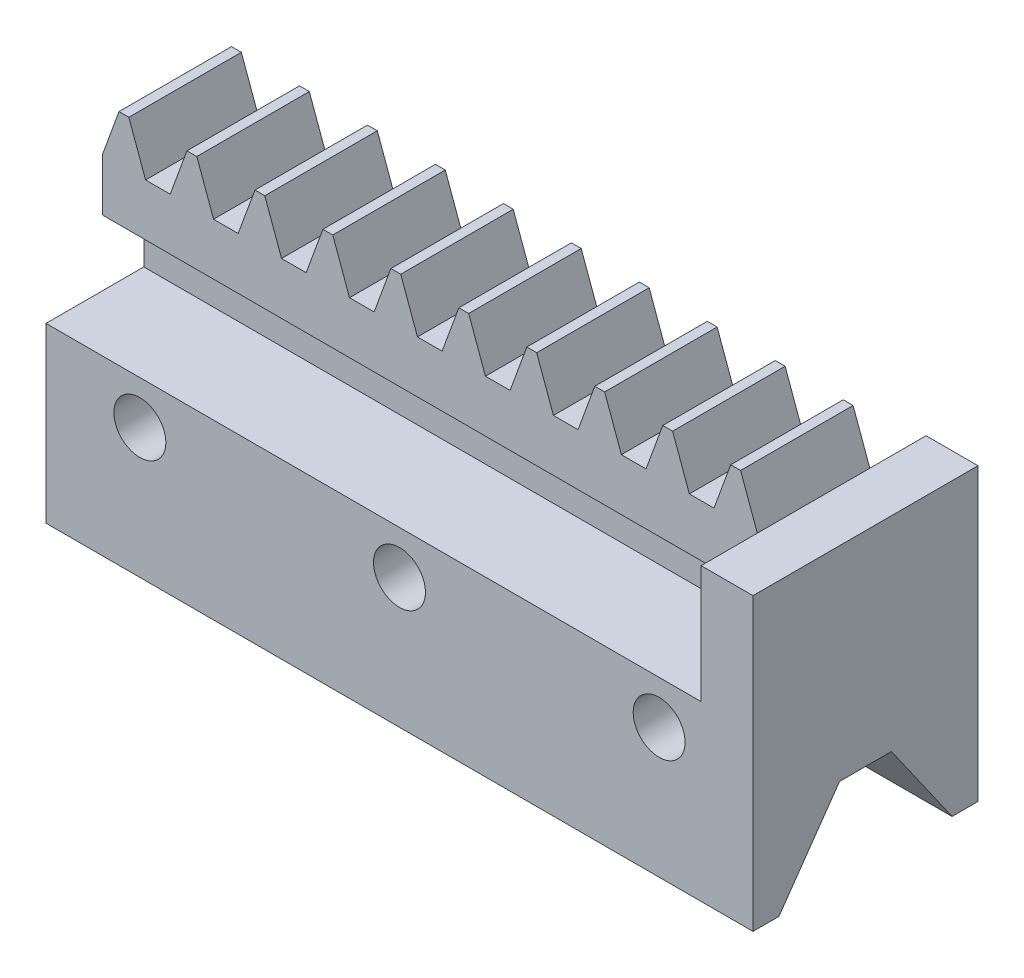
SolidWorks part; units mm, degrees
ref_plane "Plan de face" through (0, 0, 0) normal (0, 0, 1) x (1, 0, 0)
ref_plane "Plan de dessus" through (0, 0, 0) normal (0, 1, 0) x (1, 0, 0)
ref_plane "Plan de droite" through (0, 0, 0) normal (1, 0, 0) x (0, 0, -1)
sketch "Esquisse1" plane through (0, 0, 0) normal (0, 0, 1) x (1, 0, 0)
  circle A1 centre (0, 0) radius 2.5
  arc A192 (-2.7975, 7.3493) -> (-3.2186, 7.1749) centre (0, 0) ccw
  arc A193 (-3.7466, 7.3576) -> (-3.2186, 7.1749) centre (-3.3855, 7.5469) ccw
  arc A194 (-3.7466, 7.3576) -> (-5.4988, 8.9274) centre (-6.7243, 5.7967) ccw
  arc A195 (-5.4988, 8.9274) -> (-6.1435, 8.4966) centre (0, 0) ccw
  arc A196 (-6.1435, 8.4966) -> (-5.3638, 6.2771) centre (-2.7822, 8.4307) ccw
  arc A197 (-5.397, 5.7193) -> (-5.3638, 6.2771) centre (-5.6769, 6.0159) ccw
  arc A198 (-5.397, 5.7193) -> (-5.7193, 5.397) centre (0, 0) ccw
  arc A199 (-6.2771, 5.3638) -> (-5.7193, 5.397) centre (-6.0159, 5.6769) ccw
  arc A200 (-6.2771, 5.3638) -> (-8.4966, 6.1435) centre (-8.4307, 2.7822) ccw
  arc A201 (-8.4966, 6.1435) -> (-8.9274, 5.4988) centre (0, 0) ccw
  arc A202 (-8.9274, 5.4988) -> (-7.3576, 3.7466) centre (-5.7967, 6.7243) ccw
  arc A203 (-7.1749, 3.2186) -> (-7.3576, 3.7466) centre (-7.5469, 3.3855) ccw
  arc A204 (-7.1749, 3.2186) -> (-7.3493, 2.7975) centre (0, 0) ccw
  arc A205 (-7.8519, 2.5534) -> (-7.3493, 2.7975) centre (-7.7304, 2.9426) ccw
  arc A206 (-7.8519, 2.5534) -> (-10.2009, 2.4244) centre (-8.8537, -0.6559) ccw
  arc A207 (-10.2009, 2.4244) -> (-10.3521, 1.6639) centre (0, 0) ccw
  arc A208 (-10.3521, 1.6639) -> (-8.2313, 0.6458) centre (-7.9287, 3.9941) ccw
  arc A209 (-7.8604, 0.2279) -> (-8.2313, 0.6458) centre (-8.268, 0.2397) ccw
  arc A210 (-7.8604, 0.2279) -> (-7.8604, -0.2279) centre (0, 0) ccw
  arc A211 (-8.2313, -0.6458) -> (-7.8604, -0.2279) centre (-8.268, -0.2397) ccw
  arc A212 (-8.2313, -0.6458) -> (-10.3521, -1.6639) centre (-7.9287, -3.9941) ccw
  arc A213 (-10.3521, -1.6639) -> (-10.2009, -2.4244) centre (0, 0) ccw
  arc A214 (-10.2009, -2.4244) -> (-7.8519, -2.5534) centre (-8.8537, 0.6559) ccw
  arc A215 (-7.3493, -2.7975) -> (-7.8519, -2.5534) centre (-7.7304, -2.9426) ccw
  arc A216 (-7.3493, -2.7975) -> (-7.1749, -3.2186) centre (0, 0) ccw
  arc A217 (-7.3576, -3.7466) -> (-7.1749, -3.2186) centre (-7.5469, -3.3855) ccw
  arc A218 (-7.3576, -3.7466) -> (-8.9274, -5.4988) centre (-5.7967, -6.7243) ccw
  arc A219 (-8.9274, -5.4988) -> (-8.4966, -6.1435) centre (0, 0) ccw
  arc A220 (-8.4966, -6.1435) -> (-6.2771, -5.3638) centre (-8.4307, -2.7822) ccw
  arc A221 (-5.7193, -5.397) -> (-6.2771, -5.3638) centre (-6.0159, -5.6769) ccw
  arc A222 (-5.7193, -5.397) -> (-5.397, -5.7193) centre (0, 0) ccw
  arc A223 (-5.3638, -6.2771) -> (-5.397, -5.7193) centre (-5.6769, -6.0159) ccw
  arc A224 (-5.3638, -6.2771) -> (-6.1435, -8.4966) centre (-2.7822, -8.4307) ccw
  arc A225 (-6.1435, -8.4966) -> (-5.4988, -8.9274) centre (0, 0) ccw
  arc A226 (-5.4988, -8.9274) -> (-3.7466, -7.3576) centre (-6.7243, -5.7967) ccw
  arc A227 (-3.2186, -7.1749) -> (-3.7466, -7.3576) centre (-3.3855, -7.5469) ccw
  arc A228 (-3.2186, -7.1749) -> (-2.7975, -7.3493) centre (0, 0) ccw
  arc A229 (-2.5534, -7.8519) -> (-2.7975, -7.3493) centre (-2.9426, -7.7304) ccw
  arc A230 (-2.5534, -7.8519) -> (-2.4244, -10.2009) centre (0.6559, -8.8537) ccw
  arc A231 (-2.4244, -10.2009) -> (-1.6639, -10.3521) centre (0, 0) ccw
  arc A232 (-1.6639, -10.3521) -> (-0.6458, -8.2313) centre (-3.9941, -7.9287) ccw
  arc A233 (-0.2279, -7.8604) -> (-0.6458, -8.2313) centre (-0.2397, -8.268) ccw
  arc A234 (-0.2279, -7.8604) -> (0.2279, -7.8604) centre (0, 0) ccw
  arc A235 (0.6458, -8.2313) -> (0.2279, -7.8604) centre (0.2397, -8.268) ccw
  arc A236 (0.6458, -8.2313) -> (1.6639, -10.3521) centre (3.9941, -7.9287) ccw
  arc A237 (1.6639, -10.3521) -> (2.4244, -10.2009) centre (0, 0) ccw
  arc A238 (2.4244, -10.2009) -> (2.5534, -7.8519) centre (-0.6559, -8.8537) ccw
  arc A239 (2.7975, -7.3493) -> (2.5534, -7.8519) centre (2.9426, -7.7304) ccw
  arc A240 (2.7975, -7.3493) -> (3.2186, -7.1749) centre (0, 0) ccw
  arc A241 (3.7466, -7.3576) -> (3.2186, -7.1749) centre (3.3855, -7.5469) ccw
  arc A242 (3.7466, -7.3576) -> (5.4988, -8.9274) centre (6.7243, -5.7967) ccw
  arc A243 (5.4988, -8.9274) -> (6.1435, -8.4966) centre (0, 0) ccw
  arc A244 (6.1435, -8.4966) -> (5.3638, -6.2771) centre (2.7822, -8.4307) ccw
  arc A245 (5.397, -5.7193) -> (5.3638, -6.2771) centre (5.6769, -6.0159) ccw
  arc A246 (5.397, -5.7193) -> (5.7193, -5.397) centre (0, 0) ccw
  arc A247 (6.2771, -5.3638) -> (5.7193, -5.397) centre (6.0159, -5.6769) ccw
  arc A248 (6.2771, -5.3638) -> (8.4966, -6.1435) centre (8.4307, -2.7822) ccw
  arc A249 (8.4966, -6.1435) -> (8.9274, -5.4988) centre (0, 0) ccw
  arc A250 (8.9274, -5.4988) -> (7.3576, -3.7466) centre (5.7967, -6.7243) ccw
  arc A251 (7.1749, -3.2186) -> (7.3576, -3.7466) centre (7.5469, -3.3855) ccw
  arc A252 (7.1749, -3.2186) -> (7.3493, -2.7975) centre (0, 0) ccw
  arc A253 (7.8519, -2.5534) -> (7.3493, -2.7975) centre (7.7304, -2.9426) ccw
  arc A254 (7.8519, -2.5534) -> (10.2009, -2.4244) centre (8.8537, 0.6559) ccw
  arc A255 (10.2009, -2.4244) -> (10.3521, -1.6639) centre (0, 0) ccw
  arc A256 (10.3521, -1.6639) -> (8.2313, -0.6458) centre (7.9287, -3.9941) ccw
  arc A257 (7.8604, -0.2279) -> (8.2313, -0.6458) centre (8.268, -0.2397) ccw
  arc A258 (7.8604, -0.2279) -> (7.8604, 0.2279) centre (0, 0) ccw
  arc A259 (8.2313, 0.6458) -> (7.8604, 0.2279) centre (8.268, 0.2397) ccw
  arc A260 (8.2313, 0.6458) -> (10.3521, 1.6639) centre (7.9287, 3.9941) ccw
  arc A261 (10.3521, 1.6639) -> (10.2009, 2.4244) centre (0, 0) ccw
  arc A262 (10.2009, 2.4244) -> (7.8519, 2.5534) centre (8.8537, -0.6559) ccw
  arc A263 (7.3493, 2.7975) -> (7.8519, 2.5534) centre (7.7304, 2.9426) ccw
  arc A264 (7.3493, 2.7975) -> (7.1749, 3.2186) centre (0, 0) ccw
  arc A265 (7.3576, 3.7466) -> (7.1749, 3.2186) centre (7.5469, 3.3855) ccw
  arc A266 (7.3576, 3.7466) -> (8.9274, 5.4988) centre (5.7967, 6.7243) ccw
  arc A267 (8.9274, 5.4988) -> (8.4966, 6.1435) centre (0, 0) ccw
  arc A268 (8.4966, 6.1435) -> (6.2771, 5.3638) centre (8.4307, 2.7822) ccw
  arc A269 (5.7193, 5.397) -> (6.2771, 5.3638) centre (6.0159, 5.6769) ccw
  arc A270 (5.7193, 5.397) -> (5.397, 5.7193) centre (0, 0) ccw
  arc A271 (5.3638, 6.2771) -> (5.397, 5.7193) centre (5.6769, 6.0159) ccw
  arc A272 (5.3638, 6.2771) -> (6.1435, 8.4966) centre (2.7822, 8.4307) ccw
  arc A273 (6.1435, 8.4966) -> (5.4988, 8.9274) centre (0, 0) ccw
  arc A274 (5.4988, 8.9274) -> (3.7466, 7.3576) centre (6.7243, 5.7967) ccw
  arc A275 (3.2186, 7.1749) -> (3.7466, 7.3576) centre (3.3855, 7.5469) ccw
  arc A276 (3.2186, 7.1749) -> (2.7975, 7.3493) centre (0, 0) ccw
  arc A277 (2.5534, 7.8519) -> (2.7975, 7.3493) centre (2.9426, 7.7304) ccw
  arc A278 (2.5534, 7.8519) -> (2.4244, 10.2009) centre (-0.6559, 8.8537) ccw
  arc A279 (2.4244, 10.2009) -> (1.6639, 10.3521) centre (0, 0) ccw
  arc A280 (1.6639, 10.3521) -> (0.6458, 8.2313) centre (3.9941, 7.9287) ccw
  arc A281 (0.2279, 7.8604) -> (0.6458, 8.2313) centre (0.2397, 8.268) ccw
  arc A282 (0.2279, 7.8604) -> (-0.2279, 7.8604) centre (0, 0) ccw
  arc A283 (-0.6458, 8.2313) -> (-0.2279, 7.8604) centre (-0.2397, 8.268) ccw
  arc A284 (-0.6458, 8.2313) -> (-1.6639, 10.3521) centre (-3.9941, 7.9287) ccw
  arc A285 (-1.6639, 10.3521) -> (-2.4244, 10.2009) centre (0, 0) ccw
  arc A286 (-2.4244, 10.2009) -> (-2.5534, 7.8519) centre (0.6559, 8.8537) ccw
  arc A287 (-2.7975, 7.3493) -> (-2.5534, 7.8519) centre (-2.9426, 7.7304) ccw
  point P3 (0, -7.8638)
extrude "Boss.-Extru.1" add sketch "Esquisse1" along normal blind 1
sketch "Esquisse2" plane through (0, 0, 1) normal (0, 0, 1) x (1, 0, 0)
  line L0 (0, 0) -> (0, -9.25) construction
  line L1 (-0.114, -9.25) -> (-13.3501, -9.25) construction
  line L2 (-0.015, -9.2555) -> (3.6062, -7.9375) construction
  line L3 (0.2847, -8) -> (1.2514, -10.656)
  line L4 (-0.2847, -8) -> (-1.2514, -10.656)
  line L5 (-0.2847, -8) -> (0.2847, -8)
  line L6 (1.2514, -10.656) -> (2.6755, -10.656)
  line L7 (3.6422, -8) -> (2.6755, -10.656)
  line L8 (3.6422, -8) -> (4.2115, -8)
  line L9 (4.2115, -8) -> (5.1782, -10.656)
  line L10 (5.1782, -10.656) -> (6.6024, -10.656)
  line L11 (7.5691, -8) -> (6.6024, -10.656)
  line L12 (7.5691, -8) -> (8.1384, -8)
  line L13 (8.1384, -8) -> (9.1051, -10.656)
  line L14 (9.1051, -10.656) -> (10.5293, -10.656)
  line L15 (11.496, -8) -> (10.5293, -10.656)
  line L16 (11.496, -8) -> (12.0653, -8)
  line L17 (12.0653, -8) -> (13.032, -10.656)
  line L18 (13.032, -10.656) -> (14.4561, -10.656)
  line L19 (15.4228, -8) -> (14.4561, -10.656)
  line L20 (15.4228, -8) -> (15.9922, -8)
  line L21 (15.9922, -8) -> (16.9589, -10.656)
  line L22 (16.9589, -10.656) -> (18.383, -10.656)
  line L23 (19.3497, -8) -> (18.383, -10.656)
  line L24 (19.3497, -8) -> (19.919, -8)
  line L25 (19.919, -8) -> (20.8857, -10.656)
  line L26 (20.8857, -10.656) -> (22.3099, -10.656)
  line L27 (23.2766, -8) -> (22.3099, -10.656)
  line L28 (23.2766, -8) -> (23.8459, -8)
  line L29 (23.8459, -8) -> (24.8126, -10.656)
  line L30 (24.8126, -10.656) -> (26.2368, -10.656)
  line L31 (27.2035, -8) -> (26.2368, -10.656)
  line L32 (27.2035, -8) -> (27.7728, -8)
  line L33 (27.7728, -8) -> (28.7395, -10.656)
  line L34 (28.7395, -10.656) -> (30.1636, -10.656)
  line L35 (31.1303, -8) -> (30.1636, -10.656)
  line L36 (31.1303, -8) -> (31.6997, -8)
  line L37 (31.6997, -8) -> (32.6664, -10.656)
  line L38 (32.6664, -10.656) -> (34.0905, -10.656)
  line L39 (35.0572, -8) -> (34.0905, -10.656)
  line L40 (35.0572, -8) -> (35.6265, -8)
  line L41 (35.6265, -8) -> (36.5932, -10.656)
  line L42 (36.5932, -10.656) -> (38.0174, -10.656) construction
  line L43 (-1.2514, -10.656) -> (-1.2514, -13.656)
  line L44 (-1.2514, -13.656) -> (36.5932, -13.656)
  line L45 (36.5932, -13.656) -> (36.5932, -10.656)
  circle A0 centre (0, 0) radius 9.25 construction
  circle A1 centre (0, -9.25) radius 0.845 construction
  circle A2 centre (0, -9.25) radius 0.695 construction
  arc A3 (-1.6639, -10.3521) -> (-0.6458, -8.2313) centre (-3.9941, -7.9287) ccw construction
  point P8 (0, -9.25)
  dimension "D1" = 18.5
  dimension "D3" = 0.15
  dimension "D2" = 20
  dimension "D4" = 1.25
  dimension "D5" = 1.406
  dimension "D6" = 10
  dimension "D7" = 3.9269
  dimension "D8" = 3
extrude "Boss.-Extru.2" add sketch "Esquisse2" along normal blind 6.5
sketch "Esquisse3" plane through (0, 0, 0) normal (0, 0, -1) x (-1, 0, 0)
  circle A0 centre (0, 0) radius 14.1374
extrude "Enlèv. mat.-Extru.1" cut sketch "Esquisse3" against normal up to surface (1 mm away) up to face at (17.3577, -9.4996, 1)
sketch "Esquisse4" plane through (0, -13.656, 0) normal (0, -1, 0) x (1, 0, 0)
  line L0 (-1.2514, 7.5) -> (-1.2514, 1) construction
  line L1 (-1.2514, 5.1) -> (36.5932, 5.1)
  line L2 (-1.2514, 5.1) -> (-1.2514, 3.4)
  line L3 (-1.2514, 3.4) -> (36.5932, 3.4)
  line L4 (36.5932, 5.1) -> (36.5932, 3.4)
  line L5 (36.5932, 7.5) -> (36.5932, 1) construction
  point P8 (-1.2514, 4.25)
  dimension "D1" = 1.7
extrude "Boss.-Extru.3" add sketch "Esquisse4" along normal blind 3.8 contours L2 L1 L4 L3
sketch "Esquisse5" plane through (0, -17.456, 0) normal (0, -1, 0) x (1, 0, 0)
  line L0 (-1.2514, 5.1) -> (-1.2514, 3.4) construction
  line L1 (-1.2514, 10.75) -> (36.5932, 10.75)
  line L2 (-1.2514, 10.75) -> (-1.2514, -2.25)
  line L3 (-1.2514, -2.25) -> (36.5932, -2.25)
  line L4 (36.5932, 10.75) -> (36.5932, -2.25)
  line L5 (36.5932, 7.5) -> (36.5932, 5.1) construction
  point P9 (-1.2514, 4.25)
  dimension "D1" = 13
extrude "Boss.-Extru.4" add sketch "Esquisse5" along normal blind 5
sketch "Esquisse6" plane through (36.5932, 0, 0) normal (1, 0, 0) x (0, 0, -1)
  line L0 (2.25, -22.456) -> (-10.75, -22.456) construction
  line L1 (-10.75, -10.656) -> (2.25, -10.656)
  line L2 (-10.75, -10.656) -> (-10.75, -22.456)
  line L3 (-10.75, -22.456) -> (2.25, -22.456)
  line L4 (2.25, -10.656) -> (2.25, -22.456)
  line L5 (-10.75, -22.456) -> (-10.75, -17.456) construction
  line L6 (-7.5, -10.656) -> (-1, -10.656) construction
extrude "Boss.-Extru.5" add sketch "Esquisse6" along normal blind 3
sketch "Esquisse7" plane through (-1.2514, 0, 0) normal (-1, 0, 0) x (0, 0, 1)
  line L0 (-2.25, -22.456) -> (-2.25, -27.456)
  line L1 (-2.25, -27.456) -> (-0.75, -27.456)
  line L2 (-0.75, -27.456) -> (2.751, -22.456)
  line L3 (10.75, -22.456) -> (-2.25, -22.456) construction
  line L4 (2.751, -22.456) -> (-2.25, -22.456)
  line L5 (4.25, -10.656) -> (4.25, -22.456) construction
  line L6 (7.5, -10.656) -> (1, -10.656) construction
  line L7 (9.25, -27.456) -> (5.749, -22.456)
  line L8 (10.75, -27.456) -> (9.25, -27.456)
  line L9 (10.75, -22.456) -> (10.75, -27.456)
  line L10 (5.749, -22.456) -> (10.75, -22.456)
  dimension "D1" = 125
  dimension "D2" = 5
  dimension "D3" = 1.5
extrude "Boss.-Extru.6" add sketch "Esquisse7" against normal through all
sketch "Esquisse8" plane through (0, 0, -2.25) normal (0, 0, -1) x (-1, 0, 0)
  line L0 (-34.1709, -19.956) -> (-19.1709, -19.956) construction
  line L1 (-19.1709, -19.956) -> (-4.1709, -19.956) construction
  line L2 (-39.5932, -27.456) -> (1.2514, -27.456) construction
  line L3 (1.2514, -17.456) -> (-36.5932, -17.456) construction
  circle A0 centre (-34.1709, -19.956) radius 1.5
  circle A1 centre (-4.1709, -19.956) radius 1.5
  circle A2 centre (-19.1709, -19.956) radius 1.5
  point P7 (-19.1709, -27.456)
  dimension "D1" = 3
  dimension "D2" = 2.5
  dimension "D3" = 15
extrude "Enlèv. mat.-Extru.2" cut sketch "Esquisse8" against normal through all
